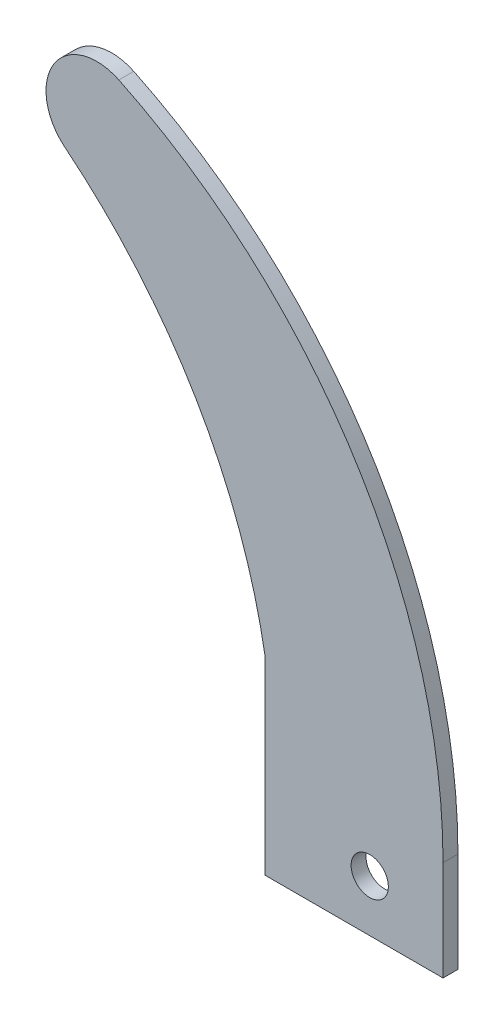
SolidWorks part; units mm, degrees
ref_plane "Спереди" through (0, 0, 0) normal (0, 0, 1) x (1, 0, 0)
ref_plane "Сверху" through (0, 0, 0) normal (0, 1, 0) x (1, 0, 0)
ref_plane "Справа" through (0, 0, 0) normal (1, 0, 0) x (0, 0, -1)
sketch "Эскиз1" plane through (0, 0, 0) normal (0, 0, 1) x (1, 0, 0)
  line L0 (-14.0337, -6.9277) -> (9.8362, -6.9277)
  line L1 (9.8362, -6.9277) -> (9.8362, 6.4684)
  line L2 (-14.0337, 18.5032) -> (-14.0337, -6.9277)
  circle A0 centre (0, 0) radius 2.5
  arc A1 (9.8362, 6.4684) -> (-33.6562, 75.6682) centre (-66.9611, 6.4684) ccw
  arc A2 (-33.6562, 75.6682) -> (-40.8982, 64.2249) centre (-36.6124, 69.5258) ccw
  arc A3 (-40.8982, 64.2249) -> (-14.0337, 18.5032) centre (-88.2614, 5.6426) cw
  point P12 (-29.5545, 74.9019)
  point P13 (-28.5181, 73.7174)
  point P14 (-33.8484, 71.4964)
  point P15 (9.8308, 13.8991)
  point P16 (-36.6617, 69.4235)
extrude "Бобышка-Вытянуть1" add sketch "Эскиз1" along normal blind 2
